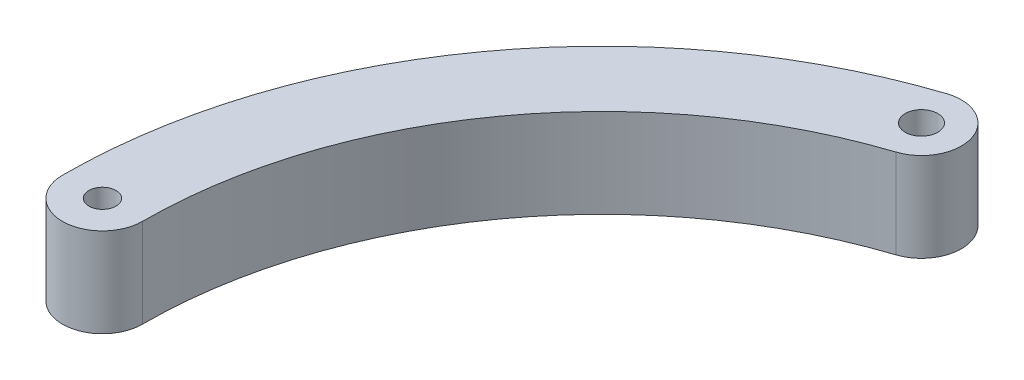
SolidWorks part; units mm, degrees
material "ABS"
ref_plane "Front Plane" through (0, 0, 0) normal (0, 0, 1) x (1, 0, 0)
ref_plane "Top Plane" through (0, 0, 0) normal (0, 1, 0) x (1, 0, 0)
ref_plane "Right Plane" through (0, 0, 0) normal (1, 0, 0) x (0, 0, -1)
sketch "Sketch1" plane through (0, 0, 0) normal (0, 1, 0) x (1, 0, 0)
  arc A2 (-33.5905, 0) -> (-10.4454, 31.9251) centre (0, 0) cw
  arc A3 (-39.4345, 0) -> (-12.2627, 37.4794) centre (0, 0) cw
  arc A4 (-10.4454, 31.9251) -> (-12.2627, 37.4794) centre (-11.3541, 34.7023) ccw
  arc A5 (-33.5905, 0) -> (-39.4345, 0) centre (-36.5125, 0) cw
  circle A6 centre (-36.5125, 0) radius 0.9922
  circle A7 centre (-11.3541, 34.7023) radius 1.1906
  dimension "D3" = 1.9844
  dimension "D4" = 2.3812
  dimension "D1" = 42.8625
  dimension "D2" = 36.5125
extrude "Boss-Extrude1" add sketch "Sketch1" along normal blind 6.51
